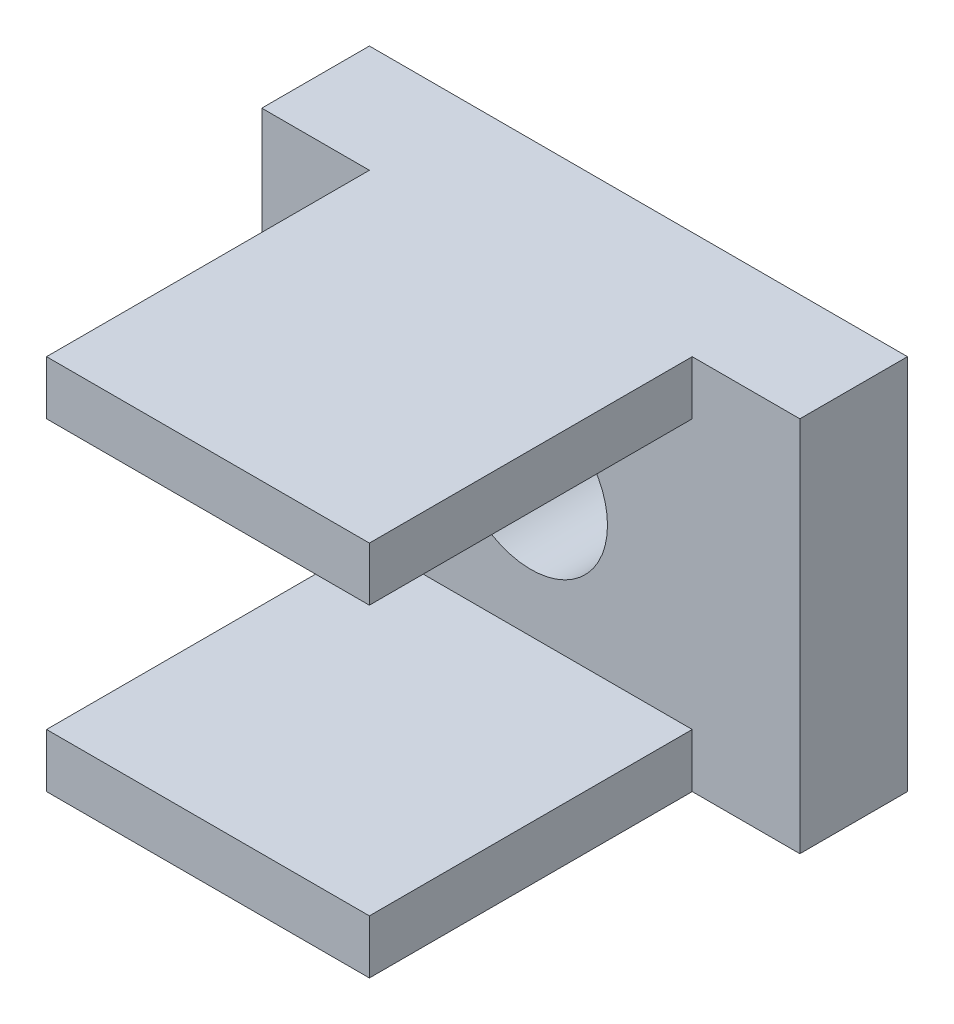
SolidWorks part; units mm, degrees
ref_plane "Front Plane" through (0, 0, 0) normal (0, 0, 1) x (1, 0, 0)
ref_plane "Top Plane" through (0, 0, 0) normal (0, 1, 0) x (1, 0, 0)
ref_plane "Right Plane" through (0, 0, 0) normal (1, 0, 0) x (0, 0, -1)
sketch "Sketch1" plane through (0, 0, 0) normal (0, 0, 1) x (1, 0, 0)
  line L1 (-5, -3.5) -> (5, -3.5)
  line L2 (-5, -3.5) -> (-5, 3.5)
  line L3 (-5, 3.5) -> (5, 3.5)
  line L4 (5, -3.5) -> (5, 3.5)
  line L5 (-5, -3.5) -> (5, 3.5) construction
  line L6 (-5, 3.5) -> (5, -3.5) construction
  point P0 (0, 0)
  dimension "D1" = 10
  dimension "D2" = 7
extrude "Boss-Extrude1" add sketch "Sketch1" against normal blind 2
sketch "Sketch2" plane through (0, 0, 0) normal (0, 0, 1) x (1, 0, 0)
  circle A0 centre (0, 0) radius 1.425
  dimension "D1" = 2.85
extrude "Cut-Extrude1" cut sketch "Sketch2" against normal blind 2
sketch "Sketch3" plane through (0, 0, 0) normal (0, 0, 1) x (1, 0, 0)
  line L0 (5, 3.5) -> (-5, 3.5) construction
  line L1 (-3, 3.5) -> (3, 3.5)
  line L2 (-3, 3.5) -> (-3, 2.5)
  line L3 (-3, 2.5) -> (3, 2.5)
  line L4 (3, 3.5) -> (3, 2.5)
  line L5 (-5, -3.5) -> (5, -3.5) construction
  line L6 (3, -3.5) -> (-3, -3.5)
  line L7 (3, -3.5) -> (3, -2.5)
  line L8 (3, -2.5) -> (-3, -2.5)
  line L9 (-3, -3.5) -> (-3, -2.5)
  point P12 (0, 2.5)
  point P13 (0, -2.5)
  dimension "D1" = 6
  dimension "D2" = 6
  dimension "D3" = 1
  dimension "D4" = 1
extrude "Boss-Extrude2" add sketch "Sketch3" along normal blind 6
